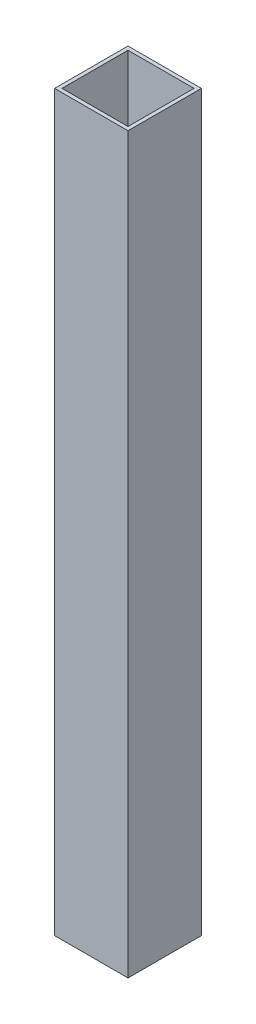
SolidWorks part; units mm, degrees
ref_plane "Front Plane" through (0, 0, 0) normal (0, 0, 1) x (1, 0, 0)
ref_plane "Top Plane" through (0, 0, 0) normal (0, 1, 0) x (1, 0, 0)
ref_plane "Right Plane" through (0, 0, 0) normal (1, 0, 0) x (0, 0, -1)
sketch "Sketch1" plane through (0, 0, 0) normal (0, 1, 0) x (1, 0, 0)
  line L0 (-9, 9) -> (9, 9)
  line L1 (-10, -10) -> (10, -10)
  line L2 (-10, -10) -> (-10, 10)
  line L3 (-10, 10) -> (10, 10)
  line L4 (10, -10) -> (10, 10)
  line L5 (-10, -10) -> (10, 10) construction
  line L6 (-10, 10) -> (10, -10) construction
  line L7 (9, -9) -> (9, 9)
  line L8 (-9, -9) -> (9, -9)
  line L9 (-9, -9) -> (-9, 9)
  point P0 (0, 0)
  dimension "D1" = 20
  dimension "D2" = 20
  dimension "D3" = 1
extrude "Boss-Extrude1" add sketch "Sketch1" along normal blind 200
sketch "Sketch2" plane through (0, 0, 10) normal (0, 0, 1) x (1, 0, 0)
  line L0 (0, 100) -> (0, 124.2111) construction
